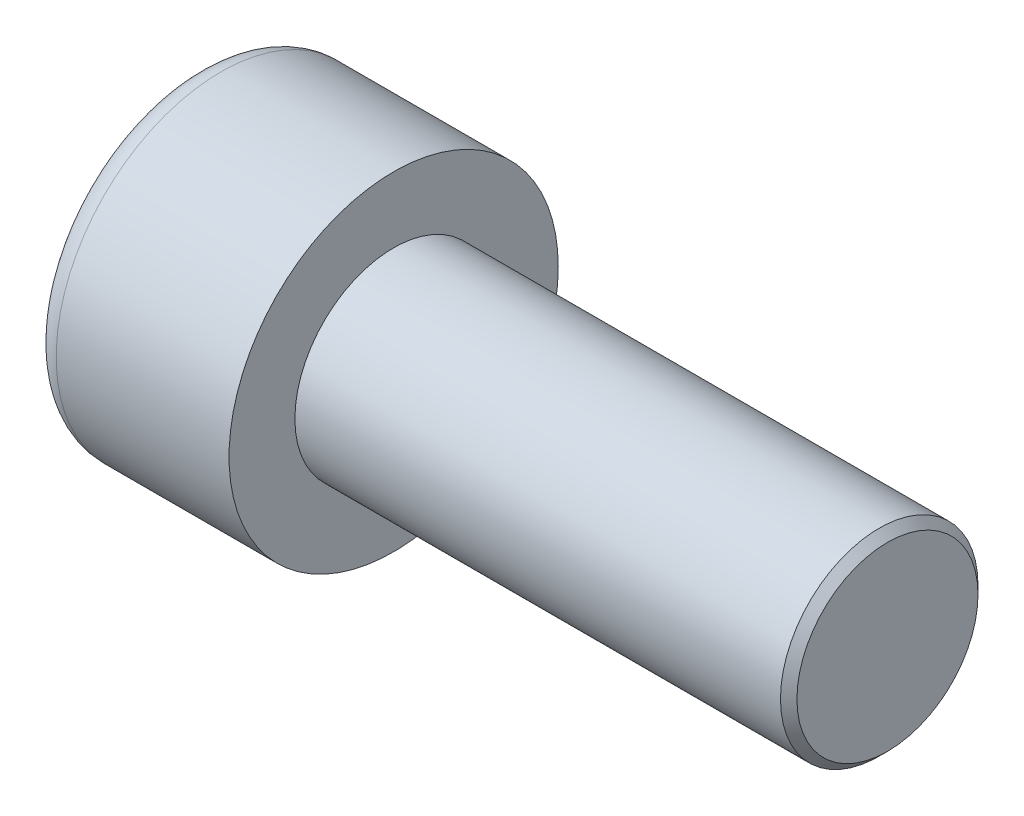
SolidWorks part; units mm, degrees
ref_plane "Front" through (0, 0, 0) normal (0, 0, 1) x (1, 0, 0)
ref_plane "Top" through (0, 0, 0) normal (0, 1, 0) x (1, 0, 0)
ref_plane "Right" through (0, 0, 0) normal (1, 0, 0) x (0, 0, -1)
sketch "Sketch1" plane through (0, 0, 0) normal (1, 0, 0) x (0, 0, -1)
  circle A0 centre (0, 0) radius 5
  dimension "dk" = 10
extrude "BaseHead" add sketch "Sketch1" along normal blind 6
sketch "Sketch2" plane through (6, 0, 0) normal (1, 0, 0) x (0, 0, -1)
  circle A0 centre (0, 0) radius 3
  dimension "d" = 6
extrude "BaseBody" add sketch "Sketch2" along normal blind 15
cosmetic thread "ThreadCosmetic1" [suppressed] parameters "b"=24, "D2"=4.917
sketch "Sketch3" plane through (0, 0, 0) normal (1, 0, 0) x (0, 0, -1)
  line L1 (2.8868, 0) -> (1.4434, 2.5)
  line L2 (1.4434, 2.5) -> (-1.4434, 2.5)
  line L3 (-1.4434, 2.5) -> (-2.8868, 0)
  line L4 (-2.8868, 0) -> (-1.4434, -2.5)
  line L5 (-1.4434, -2.5) -> (1.4434, -2.5)
  line L6 (1.4434, -2.5) -> (2.8868, 0)
  circle A0 centre (0, 0) radius 2.5 construction
  dimension "s" = 5
  dimension "e" = 5.7735
extrude "HexagonSocket" cut sketch "Sketch3" along normal blind 3
sketch "Sketch4" plane through (-4.1961, 0.75, 0) normal (0, 0, 1) x (-1, 0, 0)
  line L0 (-7.1961, 3.25) -> (-8.6395, 0.75)
  line L2 (-8.6395, 0.75) -> (-7.1961, 0.75)
  line L3 (-7.1961, 0.75) -> (-7.1961, 3.25)
  line L4 (-5.0351, 0.75) -> (0.839, 0.75) construction
  line L5 (-25.1961, 0.75) -> (-10.1961, 0.75) construction
  line L6 (-10.1961, 0.75) -> (-4.1961, 0.75) construction
  dimension "m" = 60
revolve "Cut-Revolve1" cut sketch "Sketch4" angle 360 about L4
fillet "HeadFillet" [suppressed] radius 0.25
fillet "TopFillet" radius 0.75 1 edges at (0, 0, -5)
chamfer "Chamfer1" distance 0.25 angle 45 1 edges at (21, 0, -3)
sketch "Sketch5" plane through (0, 0, 0) normal (0, 0, 1) x (1, 0, 0)
  line L0 (20.75, 2.531) -> (21.0207, 3)
  line L1 (21.0207, 3) -> (21.0207, 3.5415)
  line L2 (21.0207, 3.5415) -> (20.4792, 3.5415)
  line L3 (20.4792, 3.5415) -> (20.4792, 3)
  line L4 (20.4792, 3) -> (20.75, 2.531)
  line L5 (0, 0) -> (7.8886, 0) construction
  line L6 (20.75, -3) -> (20.75, 3) construction
  dimension "D1" = 6
  dimension "D2" = 0.5415
revolve "Cut-Revolve10" [suppressed] cut sketch "Sketch5" angle 360 about L5
pattern_linear "LPattern10" [suppressed] count 37 spacing 0.6498 along (1, 0, 0)
equation "\"r1@TopFillet\" = \"d@Sketch2\" / 8"
equation "\"D1@Chamfer1\" = \"r@HeadFillet\""
equation "\"D1@Sketch5\" = \"d@Sketch2\""
equation "\"D2@Sketch5\" =  ( \"d@Sketch2\" - \"D2@ThreadCosmetic1\" )  / 2"
equation "\"D3@LPattern10\" = \"D2@Sketch5\" * 1.2"
equation "\"D1@LPattern10\" = \"b@ThreadCosmetic1\" / \"D3@LPattern10\""
